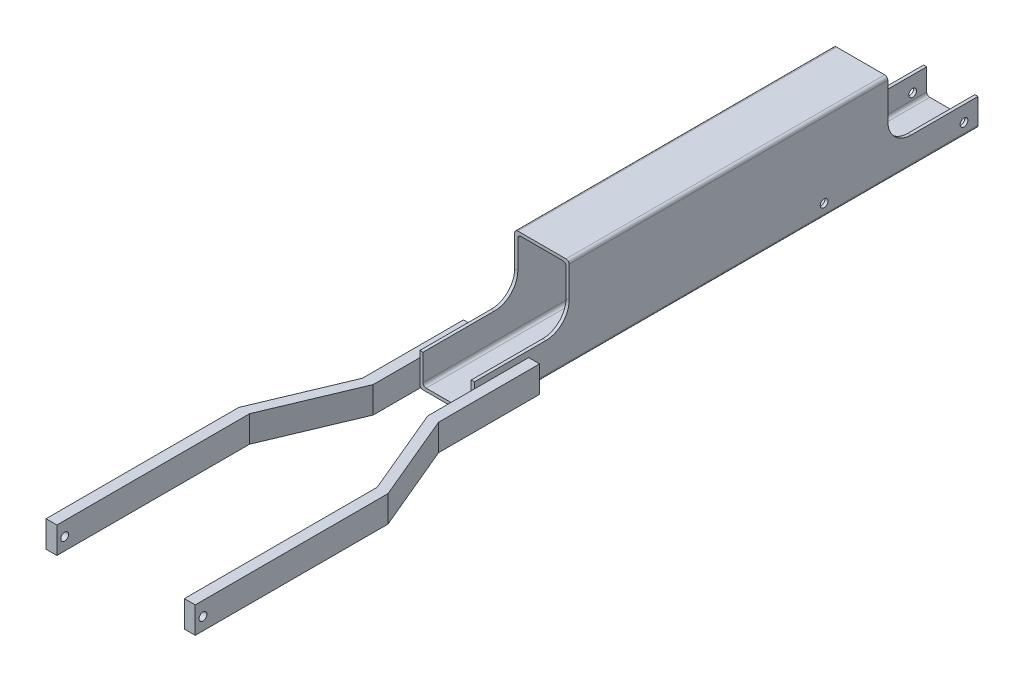
SolidWorks part; units mm, degrees
ref_plane "Front Plane" through (0, 0, 0) normal (0, 0, 1) x (1, 0, 0)
ref_plane "Top Plane" through (0, 0, 0) normal (0, 1, 0) x (1, 0, 0)
ref_plane "Right Plane" through (0, 0, 0) normal (1, 0, 0) x (0, 0, -1)
sketch "Sketch1" plane through (0, 0, 0) normal (0, 0, 1) x (1, 0, 0)
  line L1 (-17.9396, -4.0782) -> (13.0604, -4.0782)
  line L2 (-19.9396, -6.0782) -> (-19.9396, -60.0782)
  line L3 (-17.9396, -62.0782) -> (13.0604, -62.0782)
  line L4 (15.0604, -6.0782) -> (15.0604, -60.0782)
  line L5 (-15.9396, -6.0782) -> (11.0604, -6.0782)
  line L6 (-17.9396, -8.0782) -> (-17.9396, -58.0782)
  line L7 (-15.9396, -60.0782) -> (11.0604, -60.0782)
  line L8 (13.0604, -8.0782) -> (13.0604, -58.0782)
  arc A0 (11.0604, -6.0782) -> (13.0604, -8.0782) centre (11.0604, -8.0782) cw
  arc A1 (-17.9396, -8.0782) -> (-15.9396, -6.0782) centre (-15.9396, -8.0782) cw
  arc A2 (-15.9396, -60.0782) -> (-17.9396, -58.0782) centre (-15.9396, -58.0782) cw
  arc A3 (13.0604, -58.0782) -> (11.0604, -60.0782) centre (11.0604, -58.0782) cw
  arc A4 (13.0604, -62.0782) -> (15.0604, -60.0782) centre (13.0604, -60.0782) ccw
  arc A5 (-17.9396, -62.0782) -> (-19.9396, -60.0782) centre (-17.9396, -60.0782) cw
  arc A6 (-19.9396, -6.0782) -> (-17.9396, -4.0782) centre (-17.9396, -6.0782) cw
  arc A7 (13.0604, -4.0782) -> (15.0604, -6.0782) centre (13.0604, -6.0782) cw
  point P20 (-19.9396, -62.0782)
  point P23 (-19.9396, -4.0782)
  point P26 (15.0604, -4.0782)
  dimension "D7" = 2
  dimension "D1" = 58
  dimension "D2" = 35
  dimension "D3" = 2
  dimension "D4" = 2
  dimension "D5" = 2
  dimension "D6" = 2
extrude "Extrude1" add sketch "Sketch1" along normal blind 324
sketch "Sketch2" plane through (15.0604, 0, 0) normal (1, 0, 0) x (0, 0, -1)
  line L0 (0, -60.0782) -> (0, -6.0782) construction
  line L1 (0, -44.0782) -> (-43, -44.0782)
  line L2 (0, -44.0782) -> (0, -4.0782)
  line L3 (0, -4.0782) -> (-58, -4.0782)
  line L4 (-58, -29.0782) -> (-58, -4.0782)
  line L5 (-324, -4.0782) -> (0, -4.0782) construction
  line L6 (-324, -62.0782) -> (0, -62.0782) construction
  line L7 (-324, -60.0782) -> (-324, -6.0782) construction
  line L8 (-324, -41.0782) -> (-278, -41.0782)
  line L9 (-324, -41.0782) -> (-324, -4.0782)
  line L10 (-324, -4.0782) -> (-263, -4.0782)
  line L11 (-263, -26.0782) -> (-263, -4.0782)
  circle A0 centre (-9, -54.0782) radius 2.5
  circle A1 centre (-99, -54.0782) radius 2.5
  arc A2 (-263, -26.0782) -> (-278, -41.0782) centre (-278, -26.0782) cw
  arc A3 (-43, -44.0782) -> (-58, -29.0782) centre (-43, -29.0782) cw
  point P22 (-263, -41.0782)
  point P25 (-58, -44.0782)
  dimension "D4" = 5
  dimension "D5" = 5
  dimension "D11" = 15
  dimension "D1" = 58
  dimension "D2" = 40
  dimension "D3" = 8
  dimension "D6" = 8
  dimension "D7" = 9
  dimension "D8" = 99
  dimension "D9" = 61
  dimension "D10" = 37
extrude "Extrude2" cut sketch "Sketch2" against normal through all
sketch "Sketch3" plane through (0, -62.0782, 0) normal (0, -1, 0) x (1, 0, 0)
  line L0 (15.0604, 324) -> (15.0604, 289)
  line L1 (15.0604, 324) -> (15.0604, 0) construction
  line L2 (15.0604, 289) -> (22.0604, 289)
  line L4 (22.0604, 289) -> (22.0604, 324)
  line L5 (22.0604, 324) -> (22.0604, 354)
  line L6 (22.0604, 354) -> (45.5604, 410)
  line L7 (45.5604, 410) -> (45.5604, 534)
  line L8 (45.5604, 534) -> (38.5604, 534)
  line L9 (38.5604, 534) -> (38.5604, 410)
  line L10 (38.5604, 410) -> (15.0604, 354)
  line L11 (15.0604, 354) -> (15.0604, 324)
  line L12 (-19.9396, 324) -> (-19.9396, 289)
  line L13 (-19.9396, 324) -> (-19.9396, 0) construction
  line L14 (-19.9396, 289) -> (-26.9396, 289)
  line L15 (-26.9396, 289) -> (-26.9396, 324)
  line L16 (-26.9396, 324) -> (-26.9396, 354)
  line L17 (-26.9396, 354) -> (-50.4396, 410)
  line L18 (-50.4396, 410) -> (-50.4396, 534)
  line L19 (-50.4396, 534) -> (-43.4396, 534)
  line L20 (-43.4396, 534) -> (-43.4396, 410)
  line L21 (-43.4396, 410) -> (-19.9396, 354)
  line L22 (-19.9396, 354) -> (-19.9396, 324)
  line L23 (-17.9396, 0) -> (13.0604, 0) construction
  dimension "D1" = 7
  dimension "D2" = 7
  dimension "D3" = 35
  dimension "D4" = 35
  dimension "D5" = 35
  dimension "D6" = 7
  dimension "D7" = 7
  dimension "D8" = 30
  dimension "D9" = 30
  dimension "D10" = 30
  dimension "D11" = 30
  dimension "D12" = 23.5
  dimension "D13" = 23.5
  dimension "D14" = 534
  dimension "D15" = 534
  dimension "D16" = 35
  dimension "D17" = 56
  dimension "D18" = 56
  dimension "D19" = 56
extrude "Extrude3" add sketch "Sketch3" against normal blind 17
sketch "Sketch4" plane through (45.5604, 0, 0) normal (1, 0, 0) x (0, 0, -1)
  line L0 (-410, -62.0782) -> (-534, -62.0782) construction
  line L1 (-534, -45.0782) -> (-534, -62.0782) construction
  circle A0 centre (-529, -54.0782) radius 2.5
  dimension "D2" = 5
  dimension "D1" = 8
  dimension "D3" = 5
extrude "Extrude4" cut sketch "Sketch4" against normal through all
